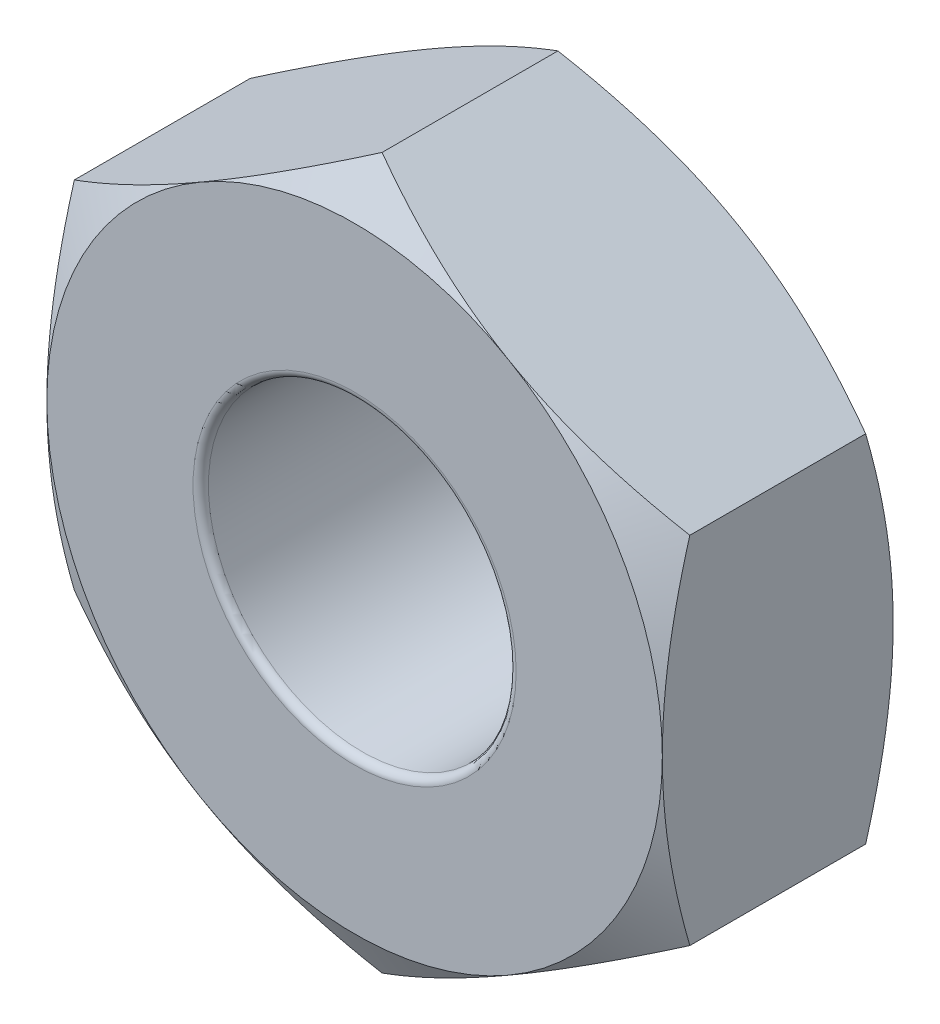
SolidWorks part; units mm, degrees
ref_plane "Front Plane" through (0, 0, 0) normal (0, 0, 1) x (1, 0, 0)
ref_plane "Top Plane" through (0, 0, 0) normal (0, 1, 0) x (1, 0, 0)
ref_plane "Right Plane" through (0, 0, 0) normal (1, 0, 0) x (0, 0, -1)
sketch "Sketch1" plane through (0, 0, 0) normal (0, 0, 1) x (1, 0, 0)
  line L1 (0, -2.3094) -> (2, -1.1547)
  line L2 (2, -1.1547) -> (2, 1.1547)
  line L3 (2, 1.1547) -> (0, 2.3094)
  line L4 (0, 2.3094) -> (-2, 1.1547)
  line L5 (-2, 1.1547) -> (-2, -1.1547)
  line L6 (-2, -1.1547) -> (0, -2.3094)
  circle A0 centre (0, 0) radius 1
  circle A1 centre (0, 0) radius 2 construction
  dimension "D1" = 2
  dimension "D2" = 4
extrude "Boss-Extrude1" add sketch "Sketch1" along normal blind 1.5
sketch "Sketch2" plane through (0, 0, 1.5) normal (0, 0, 1) x (1, 0, 0)
  circle A0 centre (0, 0) radius 2 construction
  circle A1 centre (0, 0) radius 2
extrude "Cut-Extrude1" cut sketch "Sketch2" against normal blind 2 draft 60 flip side to cut
sketch "Sketch3" plane through (0, 0, 0) normal (0, 0, -1) x (-1, 0, 0)
  circle A1 centre (0, 0) radius 2
  circle A2 centre (0, 0) radius 2
  dimension "D1" = 0
extrude "Cut-Extrude2" cut sketch "Sketch3" against normal blind 2 draft 60 flip side to cut
fillet "Fillet1" radius 0.05 2 edges at (1, 0, 0) (1, 0, 1.5)
